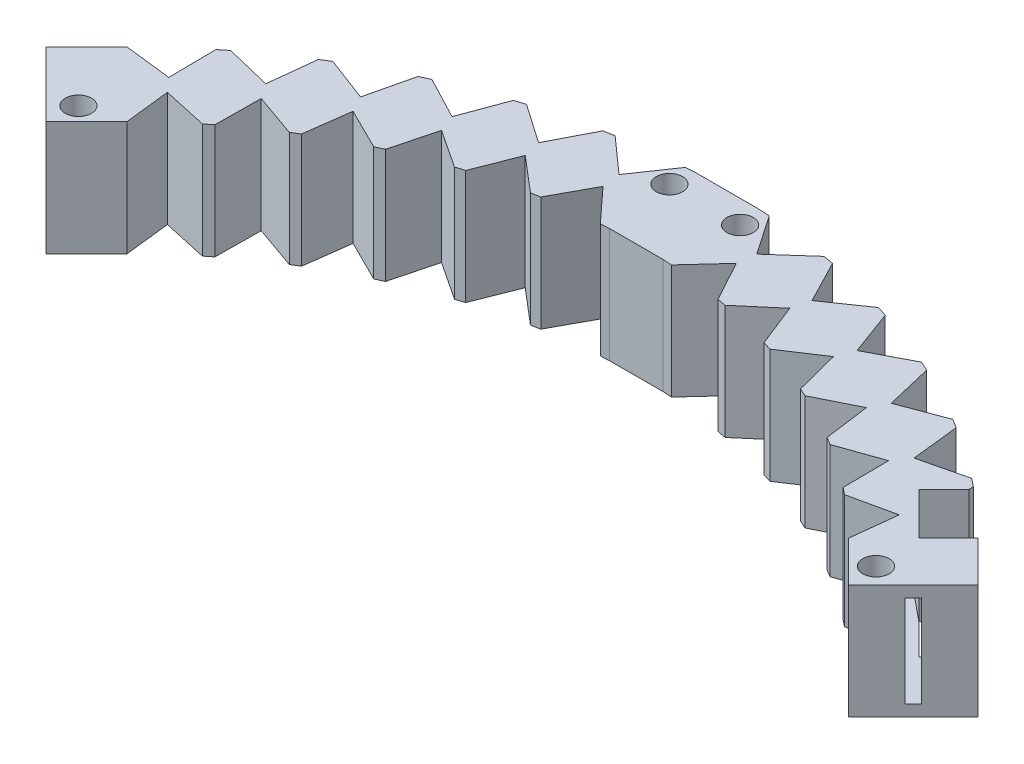
SolidWorks part; units mm, degrees
ref_plane "Front Plane" through (0, 0, 0) normal (0, 0, 1) x (1, 0, 0)
ref_plane "Top Plane" through (0, 0, 0) normal (0, 1, 0) x (1, 0, 0)
ref_plane "Right Plane" through (0, 0, 0) normal (1, 0, 0) x (0, 0, -1)
sketch "Sketch1" plane through (0, 0, 0) normal (0, 1, 0) x (1, 0, 0)
  line L0 (0, 0) -> (-28.3267, 28.3267) construction
  line L1 (-28.3267, 28.3267) -> (0, 0) construction
  line L2 (0, 0) -> (28.3267, 28.3267) construction
  line L3 (0, 0) -> (0, 40.06) construction
  line L4 (-31.5087, 31.5087) -> (-37.1655, 37.1655)
  line L5 (31.5087, 31.5087) -> (37.1655, 37.1655)
  line L6 (28.3267, 28.3267) -> (31.5087, 31.5087) construction
  line L7 (-28.3267, 28.3267) -> (-31.5087, 31.5087) construction
  arc A1 (37.1655, 37.1655) -> (-37.1655, 37.1655) centre (0, 0) ccw
  arc A2 (31.5087, 31.5087) -> (-31.5087, 31.5087) centre (0, 0) ccw
  arc A3 (-31.5087, 31.5087) -> (31.5087, 31.5087) centre (0, 0) ccw construction
  arc A4 (0, 40.06) -> (-28.3267, 28.3267) centre (0, 0) ccw construction
  dimension "D5" = 8
  dimension "D1" = 90
  dimension "D2" = 45
  dimension "D3" = 44.56
extrude "Boss-Extrude1" add sketch "Sketch1" along normal blind 10
sketch "Sketch2" plane through (0, 0, 0) normal (0, 1, 0) x (1, 0, 0)
  circle A0 centre (0, 0) radius 3.6198
sketch "Sketch3" plane through (0, 10, 0) normal (0, 1, 0) x (1, 0, 0)
  line L0 (0, 0) -> (-29.8165, 33.1145)
  line L1 (-37.1655, 37.1655) -> (-31.5087, 31.5087) construction
  line L2 (0, 0) -> (-28.0425, 34.6296)
  line L3 (-37.1655, 37.1655) -> (-33.464, 37.1655) construction
  line L4 (-33.464, 37.1655) -> (-33.0771, 40.8468) construction
  line L5 (-31.5087, 31.5087) -> (-31.5087, 34.9939) construction
  line L6 (-31.5087, 34.9939) -> (-28.0425, 34.6296) construction
  line L7 (-31.0633, 38.3599) -> (-33.0771, 40.8468) construction
  line L8 (-30.0563, 37.1165) -> (-31.0633, 38.3599) construction
  line L9 (-28.0425, 34.6296) -> (-30.0563, 37.1165) construction
  line L10 (-31.5087, 34.9939) -> (-33.464, 37.1655) construction
  line L11 (-33.464, 37.1655) -> (-33.0283, 36.6816)
  line L12 (-31.9577, 35.4926) -> (-31.5087, 31.5087)
  line L13 (-28.0425, 34.6296) -> (-31.9577, 35.4926)
  line L14 (-33.0283, 36.6816) -> (-35.1695, 39.0597) construction
  line L15 (-33.0283, 36.6816) -> (-33.0771, 40.8468)
  line L16 (-37.1655, 37.1655) -> (-33.0283, 36.6816)
  arc A0 (-33.0771, 40.8468) -> (-37.1655, 37.1655) centre (0, 0) ccw
  arc A1 (-28.0425, 34.6296) -> (-31.5087, 31.5087) centre (0, 0) ccw
  arc A2 (-33.5666, 36.1897) -> (-32.4828, 37.1655) centre (0, 0) ccw
  arc A3 (-32.4016, 35.0878) -> (-31.5087, 35.8918) centre (0, 0) ccw
  arc A4 (-33.0771, 40.8468) -> (-37.1655, 37.1655) centre (0, 0) ccw
  arc A5 (-28.0425, 34.6296) -> (-31.5087, 31.5087) centre (0, 0) ccw
  arc A6 (-37.1655, 37.1655) -> (50.2634, 15.3671) centre (0, 0) ccw construction
  arc A7 (-37.1655, 37.1655) -> (50.2634, 15.3671) centre (0, 0) ccw construction
  arc A8 (-32.4828, 37.1655) -> (-31.0633, 38.3599) centre (0, 0) ccw construction
  arc A9 (-31.5087, 35.8918) -> (-28.9688, 37.9714) centre (0, 0) ccw construction
  arc A10 (-31.5087, 31.5087) -> (42.6129, 13.0281) centre (0, 0) ccw construction
  arc A11 (-31.5087, 31.5087) -> (42.6129, 13.0281) centre (0, 0) ccw construction
  arc A12 (42.6129, 13.0281) -> (-28.0425, 34.6296) centre (0, 0) ccw construction
  arc A13 (42.6129, 13.0281) -> (-28.0425, 34.6296) centre (0, 0) ccw construction
  arc A14 (50.2634, 15.3671) -> (-33.0771, 40.8468) centre (0, 0) ccw construction
  arc A15 (50.2634, 15.3671) -> (-33.0771, 40.8468) centre (0, 0) ccw construction
  arc A16 (-31.0633, 38.3599) -> (-33.5666, 36.1897) centre (0, 0) ccw construction
  arc A17 (-30.0563, 37.1165) -> (-32.4016, 35.0878) centre (0, 0) ccw construction
  arc M3 (37.1655, 37.1655) -> (-37.1655, 37.1655) centre (0, 0) ccw
  arc M5 (-31.5087, 31.5087) -> (31.5087, 31.5087) centre (0, 0) cw
  dimension "D1" = 3.2
  dimension "D2" = 3.2
  dimension "D3" = 3
  dimension "D4" = 3
extrude "Cut-Extrude1" cut sketch "Sketch3" against normal blind 10 contours A2 L4 L3 M3 | L6 A3 L5 M5
pattern_circular "CirPattern1" count 13 every 7 about axis through (0, 0, 0) along (0, 1, 0) of "Cut-Extrude1"
sketch "Sketch4" plane through (0, 10, 0) normal (0, 1, 0) x (1, 0, 0)
  line L0 (33.9836, 33.9836) -> (34.6907, 34.6907)
  line L1 (-33.9836, 33.9836) -> (-34.6907, 34.6907)
  line L2 (0, 0) -> (31.5087, 31.5087) construction
  line L3 (0, 0) -> (-31.5087, 31.5087) construction
  line L4 (-34.6907, 34.6907) -> (-37.1655, 37.1655) construction
  line L5 (-31.5087, 31.5087) -> (-33.9836, 33.9836) construction
  line L6 (31.5087, 31.5087) -> (33.9836, 33.9836) construction
  line L7 (34.6907, 34.6907) -> (37.1655, 37.1655) construction
  arc A0 (37.1655, 37.1655) -> (-37.1655, 37.1655) centre (0, 0) ccw construction
  arc A1 (34.6907, 34.6907) -> (-34.6907, 34.6907) centre (0, 0) ccw
  arc A2 (33.9836, 33.9836) -> (-33.9836, 33.9836) centre (0, 0) ccw
  arc A3 (31.5087, 31.5087) -> (-31.5087, 31.5087) centre (0, 0) ccw construction
  arc A4 (-37.1655, 37.1655) -> (37.1655, 37.1655) centre (0, 0) ccw construction
  arc A5 (-34.6907, 34.6907) -> (34.6907, 34.6907) centre (0, 0) ccw construction
  arc A6 (-33.9836, 33.9836) -> (33.9836, 33.9836) centre (0, 0) ccw construction
  arc A7 (-30.7823, 32.2187) -> (-31.5087, 31.5087) centre (0, 0) ccw construction
  arc A8 (-31.5087, 31.5087) -> (31.5087, 31.5087) centre (0, 0) ccw construction
  dimension "D1" = 3.5
extrude "Cut-Extrude2" cut sketch "Sketch4" against normal blind 8 from offset 1 offset against normal yes
sketch "Sketch5" plane through (0, 0, 0) normal (-0.7071, 0, 0.7071) x (0.7071, 0, 0.7071)
  line L1 (-49.06, 9) -> (-48.0764, 9)
  line L2 (-49.06, 9) -> (-49.06, 1.1142)
  line L3 (-49.06, 1.1142) -> (-48.0764, 1.1142)
  line L4 (-48.0764, 9) -> (-48.0764, 1.1142)
  line L5 (-52.56, 10) -> (-44.56, 10)
  line L6 (-52.56, 10) -> (-52.56, 0)
  line L7 (-52.56, 0) -> (-44.56, 0)
  line L8 (-44.56, 10) -> (-44.56, 0)
extrude "Boss-Extrude2" add sketch "Sketch5" along normal blind 5
sketch "Sketch6" plane through (0, 0, 0) normal (0.7071, 0, 0.7071) x (0.7071, 0, -0.7071)
  line L1 (48.06, 9) -> (49.06, 9)
  line L2 (48.06, 9) -> (48.06, 1)
  line L3 (48.06, 1) -> (49.06, 1)
  line L4 (49.06, 9) -> (49.06, 1)
  line L5 (52.56, 10) -> (44.56, 10)
  line L6 (52.56, 10) -> (52.56, 0)
  line L7 (52.56, 0) -> (44.56, 0)
  line L8 (44.56, 10) -> (44.56, 0)
extrude "Boss-Extrude3" add sketch "Sketch6" along normal blind 5
sketch "Sketch7" plane through (0, 10, 0) normal (0, 1, 0) x (1, 0, 0)
  line L0 (-2.7203, 44.4769) -> (-2.7724, 45.329) construction
  line L1 (3.2087, 52.462) -> (3.1568, 51.6136) construction
  line L2 (0, 0) -> (0, 47.76) construction
  line L3 (-2.9129, 47.6247) -> (-3.0164, 49.3178) construction
  line L4 (-3.1568, 51.6136) -> (-3.2087, 52.462) construction
  line L5 (-3.0164, 49.3178) -> (-3.1568, 51.6136) construction
  line L6 (3.1568, 51.6136) -> (3.0164, 49.3178) construction
  line L7 (2.7724, 45.329) -> (2.7203, 44.4769) construction
  line L8 (3.0164, 49.3178) -> (2.9129, 47.6247) construction
  line L9 (2.9129, 47.6247) -> (2.7724, 45.329) construction
  line L10 (-2.7724, 45.329) -> (-2.9129, 47.6247) construction
  circle A6 centre (-3.0866, 50.4657) radius 1.15
  circle A7 centre (3.0866, 50.4657) radius 1.15
  dimension "D1" = 2
  dimension "D5" = 2.3
  dimension "D6" = 2.3
  dimension "D2" = 2
extrude "Cut-Extrude3" cut sketch "Sketch7" against normal blind 20
sketch "Sketch9" plane through (0, 10, 0) normal (0, 1, 0) x (1, 0, 0)
  line L0 (35.0442, 27.9731) -> (31.5087, 31.5087) construction
  line L1 (40.7011, 33.63) -> (35.0442, 27.9731) construction
  circle A0 centre (34.8321, 30.5894) radius 1.15
  dimension "D1" = 2.3
  dimension "D3" = 2
  dimension "D2" = 1.7
extrude "Cut-Extrude4" cut sketch "Sketch9" against normal blind 26
sketch "Sketch10" plane through (0, 10, 0) normal (0, 1, 0) x (1, 0, 0)
  line L0 (-35.0442, 27.9731) -> (-40.7011, 33.63) construction
  line L2 (-35.0442, 27.9731) -> (-31.5087, 31.5087) construction
  circle A0 centre (-34.8321, 30.5894) radius 1.15
  dimension "D1" = 2.3
  dimension "D2" = 2
  dimension "D3" = 1.7
extrude "Cut-Extrude5" cut sketch "Sketch10" against normal blind 26
sketch "Sketch11" plane through (0, 10, 0) normal (0, 1, 0) x (1, 0, 0)
  line L0 (-2.7508, 52.488) -> (2.7508, 52.488)
  line L1 (2.7508, 52.488) -> (0, 49.36)
  line L2 (0, 49.36) -> (-2.7508, 52.488)
  line L3 (0, 47.76) -> (-2.3321, 44.4989)
  line L4 (-2.3321, 44.4989) -> (2.3321, 44.4989)
  line L5 (2.3321, 44.4989) -> (0, 47.76)
extrude "Boss-Extrude4" add sketch "Sketch11" against normal up to surface (10 mm away) up to face at (-34.8321, 0, -29.4394)
sketch "Sketch13" plane through (0, 10, 0) normal (0, 1, 0) x (1, 0, 0)
  line L0 (37.1655, 37.1655) -> (34.9053, 34.9053)
  line L1 (33.0283, 36.6816) -> (34.9053, 34.9053)
  line L2 (33.0283, 36.6816) -> (37.1655, 37.1655)
  line L3 (34.9053, 34.9053) -> (34.7143, 34.7143) construction
sketch "Sketch14" plane through (0, 10, 0) normal (0, 1, 0) x (1, 0, 0)
  line L0 (37.1655, 37.1655) -> (34.5949, 34.5949)
  line L1 (37.1655, 37.1655) -> (33.4673, 40.8638)
  line L2 (34.5949, 34.5949) -> (30.8966, 38.2931)
  line L3 (33.4673, 40.8638) -> (30.8966, 38.2931)
extrude "Cut-Extrude7" cut sketch "Sketch14" against normal blind 26
